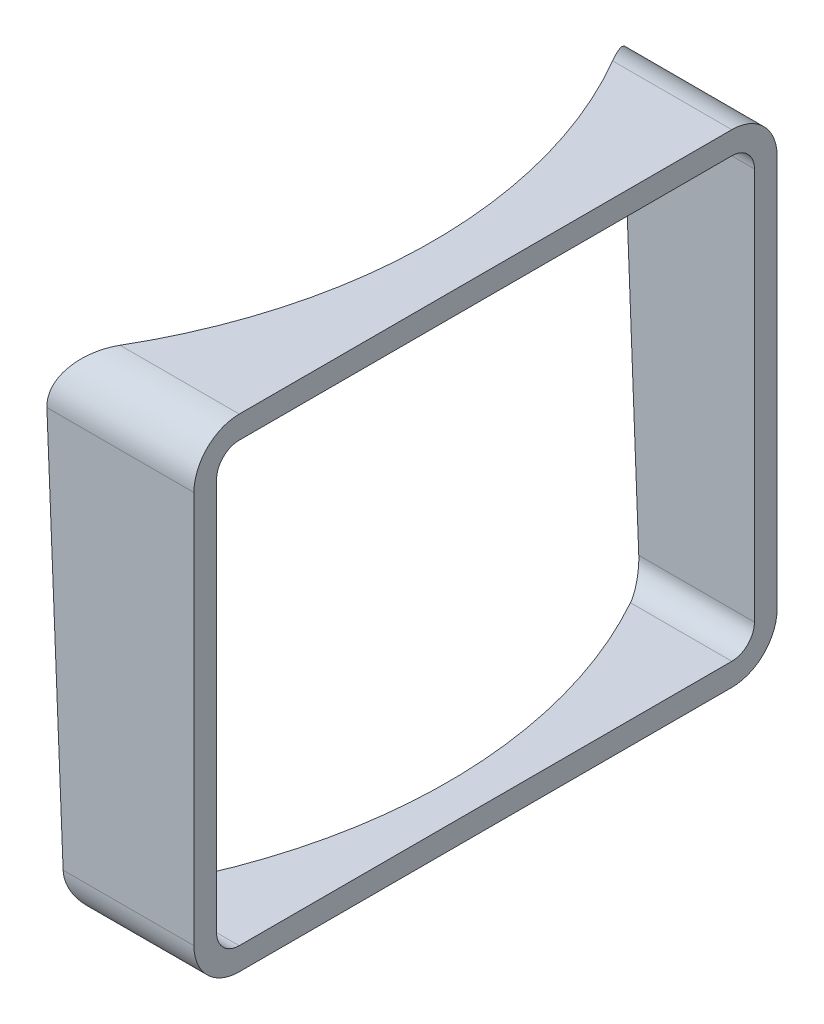
SolidWorks part; units mm, degrees
ref_plane "Front" through (0, 0, 0) normal (0, 0, 1) x (1, 0, 0)
ref_plane "Top" through (0, 0, 0) normal (0, 1, 0) x (1, 0, 0)
ref_plane "Right" through (0, 0, 0) normal (1, 0, 0) x (0, 0, -1)
sketch "Sketch1" plane through (0, 0, 0) normal (0, 1, 0) x (1, 0, 0)
  line L1 (0, 64.3692) -> (-58.4135, 64.3692)
  line L2 (0, 64.3692) -> (0, -64.3692)
  line L3 (0, -64.3692) -> (-58.4135, -64.3692)
  line L4 (-58.4135, 64.3692) -> (-58.4135, -64.3692)
extrude "Boss-Extrude1" add sketch "Sketch1" against normal blind 106.64
sketch "Sketch2" plane through (0, 0, 0) normal (0, 0, 1) x (1, 0, 0)
  line L0 (-11.6612, 0) -> (-8.0837, -106.64)
  line L1 (-58.4135, 0) -> (0, 0) construction
  line L2 (-58.4135, -106.64) -> (0, -106.64) construction
  line L3 (-119.9164, 0) -> (-119.9164, -106.64) construction
  line L4 (-11.6612, 0) -> (-119.9164, 0)
  line L5 (-119.9164, 0) -> (-119.9164, -106.64)
  line L6 (-119.9164, -106.64) -> (-8.0837, -106.64)
  line L7 (-7.878, -112.7688) -> (-8.3896, -97.5237) construction
revolve "Cut-Revolve1" cut sketch "Sketch2" angle 360 about L3
fillet "Fillet1" radius 10 4 edges at (-14.233, -106.64, 64.3692) (-14.233, -106.64, -64.3692) (-16.4386, 0, 64.3692) (-16.4386, 0, -64.3692)
shell "Shell1" thickness 5
